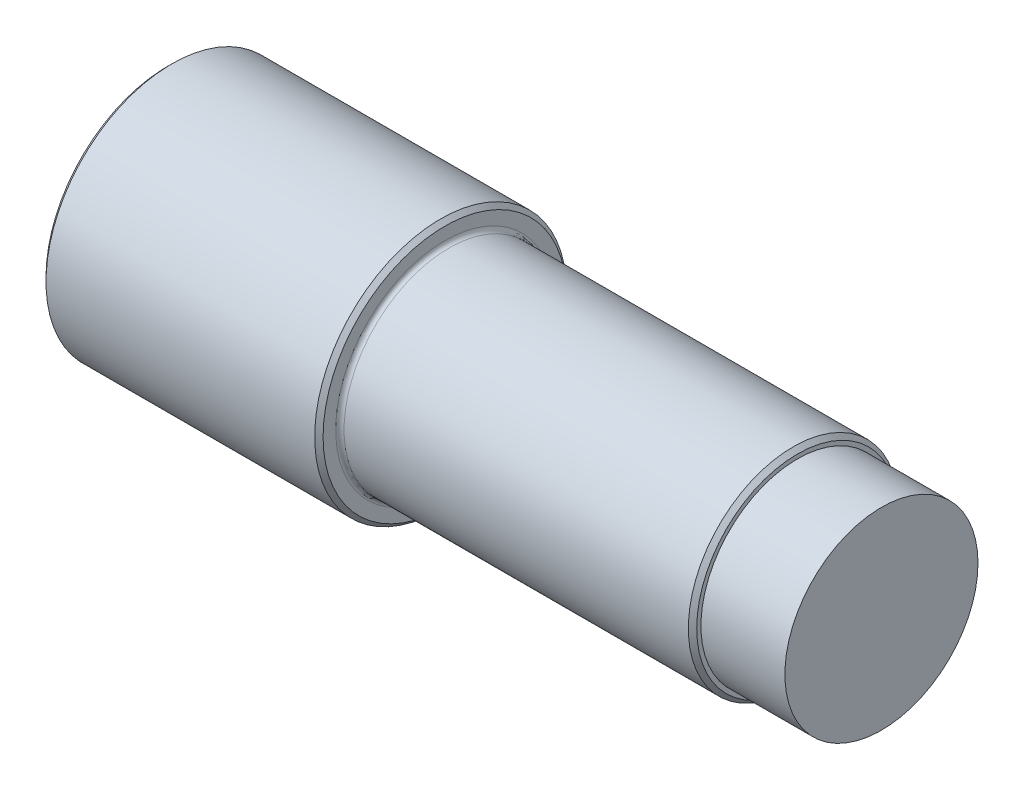
SolidWorks part; units mm, degrees
material "AISI 1045 钢，冷拔"
ref_plane "前视基准面" through (0, 0, 0) normal (0, 0, 1) x (1, 0, 0)
ref_plane "上视基准面" through (0, 0, 0) normal (0, 1, 0) x (1, 0, 0)
ref_plane "右视基准面" through (0, 0, 0) normal (1, 0, 0) x (0, 0, -1)
sketch "草图1" plane through (0, 0, 0) normal (1, 0, 0) x (0, 0, -1)
  circle A0 centre (0, 0) radius 15
  dimension "D1" = 30
extrude "凸台-拉伸1" add sketch "草图1" along normal blind 33
sketch "草图2" plane through (33, 0, 0) normal (1, 0, 0) x (0, 0, -1)
  circle A0 centre (0, 0) radius 12.5
  dimension "D1" = 25
extrude "凸台-拉伸2" add sketch "草图2" along normal blind 42
fillet "圆角1" radius 0.5 1 edges at (33, 0, -12.5)
chamfer "倒角1" distance 0.5 angle 45 3 edges at (75, 0, -12.5) (33, 0, -15) (0, 0, -15)
sketch "草图3" plane through (75, 0, 0) normal (1, 0, 0) x (0, 0, -1)
  circle A0 centre (0, 0) radius 11.5
  dimension "D1" = 23
extrude "凸台-拉伸3" add sketch "草图3" along normal blind 10 contours A0
